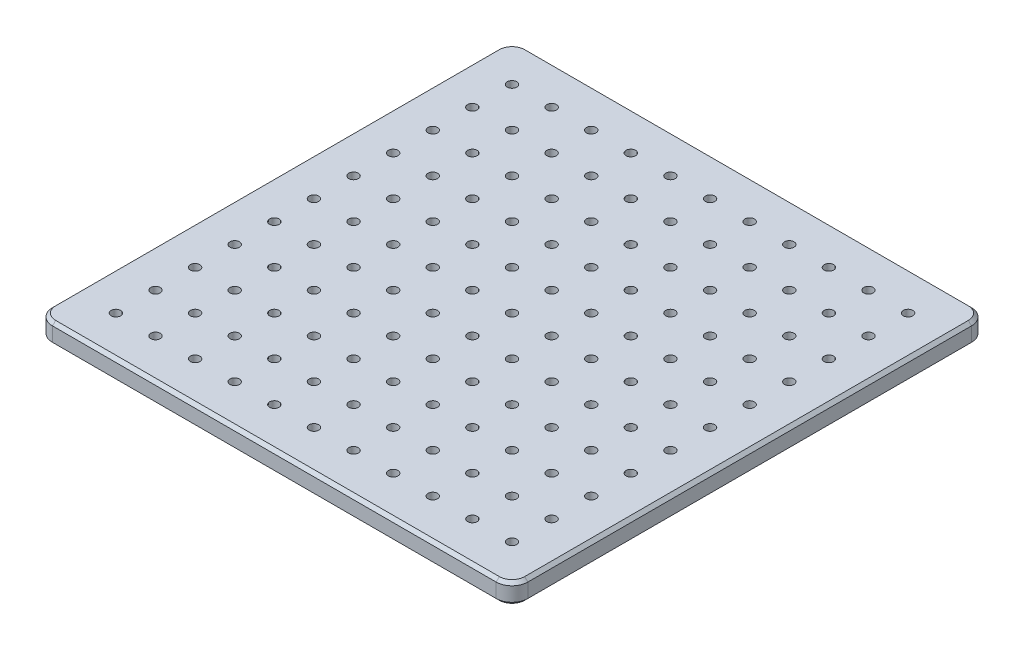
SolidWorks part; units mm, degrees
material "铸造合金钢"
ref_plane "前视基准面" through (0, 0, 0) normal (0, 0, 1) x (1, 0, 0)
ref_plane "上视基准面" through (0, 0, 0) normal (0, 1, 0) x (1, 0, 0)
ref_plane "右视基准面" through (0, 0, 0) normal (1, 0, 0) x (0, 0, -1)
sketch "草图1" plane through (0, 0, 0) normal (0, 1, 0) x (1, 0, 0)
  line L1 (-140, 150) -> (140, 150)
  line L2 (-150, 140) -> (-150, -140)
  line L3 (-140, -150) -> (140, -150)
  line L4 (150, 140) -> (150, -140)
  line L5 (-150, 150) -> (150, -150) construction
  line L6 (-150, -150) -> (150, 150) construction
  arc A0 (-140, 150) -> (-150, 140) centre (-140, 140) ccw
  arc A1 (140, 150) -> (150, 140) centre (140, 140) cw
  arc A2 (140, -150) -> (150, -140) centre (140, -140) ccw
  arc A3 (-150, -140) -> (-140, -150) centre (-140, -140) ccw
  circle A4 centre (-125, 125) radius 3
  circle A5 centre (-100, 125) radius 3
  circle A6 centre (-75, 125) radius 3
  circle A7 centre (-50, 125) radius 3
  circle A8 centre (-25, 125) radius 3
  circle A9 centre (0, 125) radius 3
  circle A10 centre (25, 125) radius 3
  circle A11 centre (50, 125) radius 3
  circle A12 centre (75, 125) radius 3
  circle A13 centre (100, 125) radius 3
  circle A14 centre (125, 125) radius 3
  circle A15 centre (125, 100) radius 3
  circle A16 centre (100, 100) radius 3
  circle A17 centre (75, 100) radius 3
  circle A18 centre (50, 100) radius 3
  circle A19 centre (25, 100) radius 3
  circle A20 centre (0, 100) radius 3
  circle A21 centre (-25, 100) radius 3
  circle A22 centre (-50, 100) radius 3
  circle A23 centre (-75, 100) radius 3
  circle A24 centre (-100, 100) radius 3
  circle A25 centre (-125, 100) radius 3
  circle A26 centre (125, 75) radius 3
  circle A27 centre (100, 75) radius 3
  circle A28 centre (75, 75) radius 3
  circle A29 centre (50, 75) radius 3
  circle A30 centre (25, 75) radius 3
  circle A31 centre (0, 75) radius 3
  circle A32 centre (-25, 75) radius 3
  circle A33 centre (-50, 75) radius 3
  circle A34 centre (-75, 75) radius 3
  circle A35 centre (-100, 75) radius 3
  circle A36 centre (-125, 75) radius 3
  circle A37 centre (125, 50) radius 3
  circle A38 centre (100, 50) radius 3
  circle A39 centre (75, 50) radius 3
  circle A40 centre (50, 50) radius 3
  circle A41 centre (25, 50) radius 3
  circle A42 centre (0, 50) radius 3
  circle A43 centre (-25, 50) radius 3
  circle A44 centre (-50, 50) radius 3
  circle A45 centre (-75, 50) radius 3
  circle A46 centre (-100, 50) radius 3
  circle A47 centre (-125, 50) radius 3
  circle A48 centre (125, 25) radius 3
  circle A49 centre (100, 25) radius 3
  circle A50 centre (75, 25) radius 3
  circle A51 centre (50, 25) radius 3
  circle A52 centre (25, 25) radius 3
  circle A53 centre (0, 25) radius 3
  circle A54 centre (-25, 25) radius 3
  circle A55 centre (-50, 25) radius 3
  circle A56 centre (-75, 25) radius 3
  circle A57 centre (-100, 25) radius 3
  circle A58 centre (-125, 25) radius 3
  circle A59 centre (125, 0) radius 3
  circle A60 centre (100, 0) radius 3
  circle A61 centre (75, 0) radius 3
  circle A62 centre (50, 0) radius 3
  circle A63 centre (25, 0) radius 3
  circle A64 centre (0, 0) radius 3
  circle A65 centre (-25, 0) radius 3
  circle A66 centre (-50, 0) radius 3
  circle A67 centre (-75, 0) radius 3
  circle A68 centre (-100, 0) radius 3
  circle A69 centre (-125, 0) radius 3
  circle A70 centre (125, -25) radius 3
  circle A71 centre (100, -25) radius 3
  circle A72 centre (75, -25) radius 3
  circle A73 centre (50, -25) radius 3
  circle A74 centre (25, -25) radius 3
  circle A75 centre (0, -25) radius 3
  circle A76 centre (-25, -25) radius 3
  circle A77 centre (-50, -25) radius 3
  circle A78 centre (-75, -25) radius 3
  circle A79 centre (-100, -25) radius 3
  circle A80 centre (-125, -25) radius 3
  circle A81 centre (125, -50) radius 3
  circle A82 centre (100, -50) radius 3
  circle A83 centre (75, -50) radius 3
  circle A84 centre (50, -50) radius 3
  circle A85 centre (25, -50) radius 3
  circle A86 centre (0, -50) radius 3
  circle A87 centre (-25, -50) radius 3
  circle A88 centre (-50, -50) radius 3
  circle A89 centre (-75, -50) radius 3
  circle A90 centre (-100, -50) radius 3
  circle A91 centre (-125, -50) radius 3
  circle A92 centre (125, -75) radius 3
  circle A93 centre (100, -75) radius 3
  circle A94 centre (75, -75) radius 3
  circle A95 centre (50, -75) radius 3
  circle A96 centre (25, -75) radius 3
  circle A97 centre (0, -75) radius 3
  circle A98 centre (-25, -75) radius 3
  circle A99 centre (-50, -75) radius 3
  circle A100 centre (-75, -75) radius 3
  circle A101 centre (-100, -75) radius 3
  circle A102 centre (-125, -75) radius 3
  circle A103 centre (125, -100) radius 3
  circle A104 centre (100, -100) radius 3
  circle A105 centre (75, -100) radius 3
  circle A106 centre (50, -100) radius 3
  circle A107 centre (25, -100) radius 3
  circle A108 centre (0, -100) radius 3
  circle A109 centre (-25, -100) radius 3
  circle A110 centre (-50, -100) radius 3
  circle A111 centre (-75, -100) radius 3
  circle A112 centre (-100, -100) radius 3
  circle A113 centre (-125, -100) radius 3
  circle A114 centre (125, -125) radius 3
  circle A115 centre (100, -125) radius 3
  circle A116 centre (75, -125) radius 3
  circle A117 centre (50, -125) radius 3
  circle A118 centre (25, -125) radius 3
  circle A119 centre (0, -125) radius 3
  circle A120 centre (-25, -125) radius 3
  circle A121 centre (-50, -125) radius 3
  circle A122 centre (-75, -125) radius 3
  circle A123 centre (-100, -125) radius 3
  circle A124 centre (-125, -125) radius 3
  point P0 (0, 0)
  dimension "D2" = 10
  dimension "D3" = 10
  dimension "D4" = 6
  dimension "D1" = 300
  dimension "D5" = 25
  dimension "D6" = 25
  dimension "D7" = 11
  dimension "D8" = 11
extrude "凸台-拉伸1" add sketch "草图1" along normal blind 13
chamfer "倒角1" distance 2 angle 45 16 edges at (0, 0, -150) (-147.0711, 0, -147.0711) (147.0711, 0, -147.0711) (-150, 0, 0) (150, 0, 0) (-147.0711, 0, 147.0711) (147.0711, 0, 147.0711) (0, 0, 150) (0, 13, -150) (-147.0711, 13, -147.0711) (147.0711, 13, -147.0711) (-150, 13, 0) (150, 13, 0) (-147.0711, 13, 147.0711) (147.0711, 13, 147.0711) (0, 13, 150)
